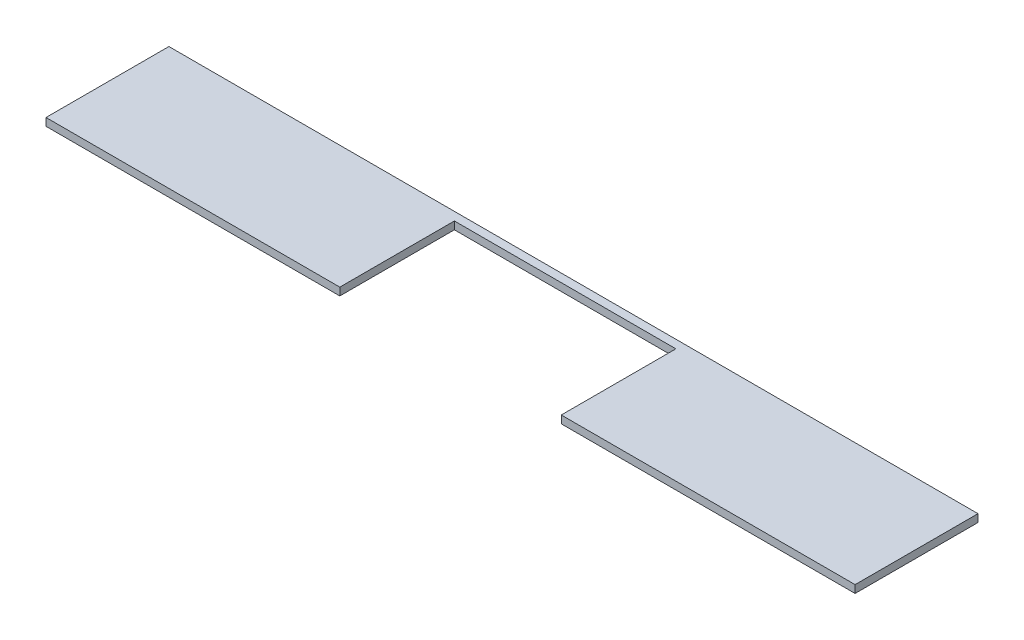
SolidWorks part; units mm, degrees
ref_plane "Front Plane" through (0, 0, 0) normal (0, 0, 1) x (1, 0, 0)
ref_plane "Top Plane" through (0, 0, 0) normal (0, 1, 0) x (1, 0, 0)
ref_plane "Right Plane" through (0, 0, 0) normal (1, 0, 0) x (0, 0, -1)
sketch "Sketch1" plane through (0, 0, 0) normal (0, 1, 0) x (1, 0, 0)
  line L1 (158, -24) -> (-158, -24)
  line L2 (158, -24) -> (158, 24)
  line L3 (158, 24) -> (-158, 24)
  line L4 (-158, -24) -> (-158, 24)
  line L5 (158, -24) -> (-158, 24) construction
  line L6 (158, 24) -> (-158, -24) construction
  point P0 (0, 0)
  dimension "D1" = 316
  dimension "D2" = 48
extrude "Boss-Extrude1" add sketch "Sketch1" along normal blind 3
sketch "Sketch2" plane through (0, 0, 0) normal (0, 1, 0) x (1, 0, 0)
  line L0 (43.25, -24) -> (-43.25, -24)
  line L1 (-158, -24) -> (158, -24) construction
  line L2 (-43.25, -24) -> (-43.25, 20.75)
  line L3 (-43.25, 20.75) -> (43.25, 20.75)
  line L4 (43.25, 20.75) -> (43.25, -24)
  point P0 (43.25, 4.7207)
  point P3 (0, -24)
  point P7 (0, -24)
  dimension "D1" = 86.5
  dimension "D2" = 44.75
  dimension "D3" = 44.75
extrude "Cut-Extrude1" cut sketch "Sketch2" along normal blind 3 contours L4 L0 L2 L3
